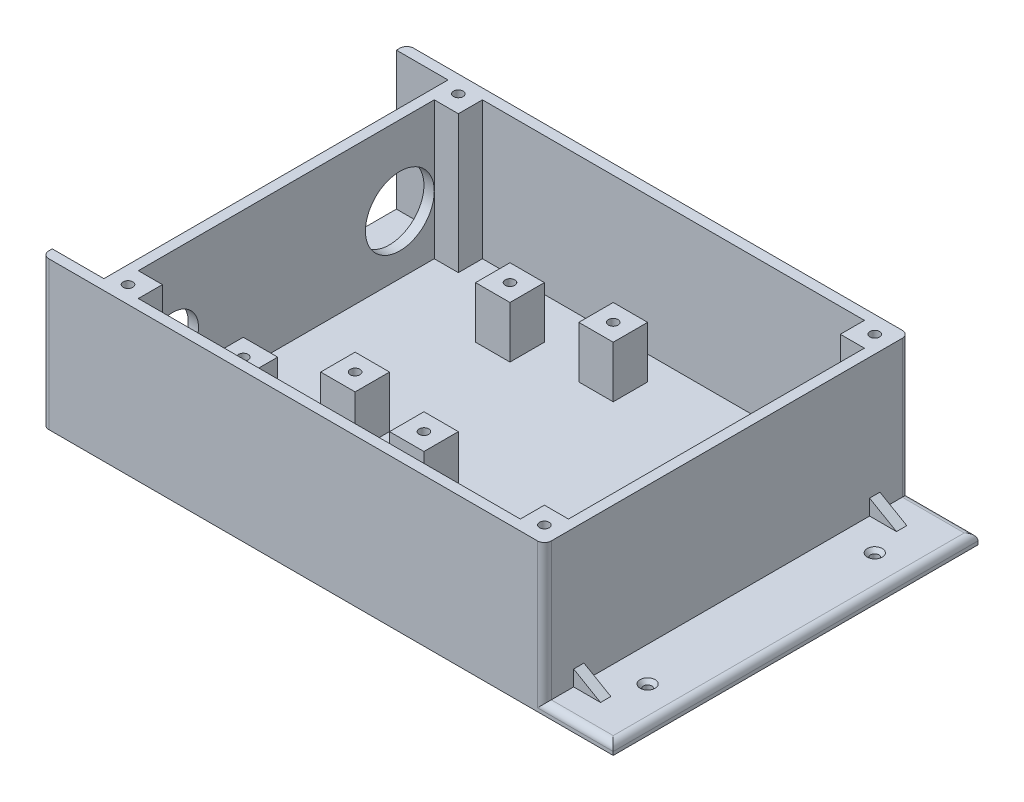
SolidWorks part; units mm, degrees
ref_plane "Front Plane" through (0, 0, 0) normal (0, 0, 1) x (1, 0, 0)
ref_plane "Top Plane" through (0, 0, 0) normal (0, 1, 0) x (1, 0, 0)
ref_plane "Right Plane" through (0, 0, 0) normal (1, 0, 0) x (0, 0, -1)
sketch "Sketch1" plane through (0, 0, 0) normal (0, 1, 0) x (1, 0, 0)
  line L1 (0, 0) -> (166, 0)
  line L2 (0, 0) -> (0, 106)
  line L3 (0, 106) -> (166, 106)
  line L4 (166, 0) -> (166, 106)
  dimension "D1" = 106
  dimension "D2" = 166
extrude "Boss-Extrude1" add sketch "Sketch1" along normal blind 43
shell "Shell1" thickness 3
sketch "Sketch2" plane through (0, 3, 0) normal (0, 1, 0) x (1, 0, 0)
  line L0 (166, 103) -> (0, 103) construction
  line L1 (18, 103) -> (15, 103)
  line L2 (18, 103) -> (18, 3)
  line L3 (18, 3) -> (15, 3)
  line L4 (15, 103) -> (15, 3)
  line L5 (0, 103) -> (0, 3) construction
  line L6 (0, 3) -> (166, 3) construction
  point P10 (16.5, 3)
  dimension "D1" = 15
  dimension "D2" = 3
extrude "Boss-Extrude2" add sketch "Sketch2" along normal blind 40
sketch "Sketch3" plane through (15, 0, 0) normal (-1, 0, 0) x (0, 0, 1)
  line L0 (-106, 0) -> (0, 0) construction
  line L1 (-106, 43) -> (-106, 0) construction
  circle A0 centre (-86, 20) radius 10
  dimension "D1" = 20
  dimension "D2" = 20
extrude "Cut-Extrude1" cut sketch "Sketch3" against normal blind 3
sketch "Sketch4" plane through (15, 0, 0) normal (-1, 0, 0) x (0, 0, 1)
  line L0 (0, 43) -> (0, 0) construction
  line L3 (-106, 0) -> (0, 0) construction
  circle A0 centre (-20, 20) radius 7.5
  dimension "D1" = 20
  dimension "D2" = 20
extrude "Cut-Extrude3" cut sketch "Sketch4" against normal blind 3
sketch "Sketch5" plane through (0, 3, 0) normal (0, 1, 0) x (1, 0, 0)
  line L1 (146, 103) -> (143, 103)
  line L2 (146, 103) -> (146, 3)
  line L3 (146, 3) -> (143, 3)
  line L4 (143, 103) -> (143, 3)
  line L5 (18, 3) -> (166, 3) construction
  line L6 (166, 103) -> (18, 103) construction
  line L7 (166, 3) -> (166, 103) construction
  point P4 (144.5, 103)
  dimension "D1" = 3
  dimension "D2" = 20
extrude "Boss-Extrude4" add sketch "Sketch5" along normal blind 40
sketch "Sketch6" plane through (166, 0, 0) normal (1, 0, 0) x (0, 0, -1)
  line L0 (106, 43) -> (106, 0) construction
  line L1 (106, 3) -> (103, 3)
  line L2 (106, 3) -> (106, 43)
  line L3 (106, 43) -> (103, 43)
  line L4 (103, 3) -> (103, 43)
  line L5 (103, 43) -> (106, 43) construction
  point P8 (104.5, 43)
  dimension "D1" = 3
  dimension "D2" = 40
extrude "Cut-Extrude4" cut sketch "Sketch6" against normal blind 20
ref_plane "Plane5" through (0, 0, -53) normal (0, 0, -1) x (-1, 0, 0)
mirror "Mirror1" about plane through (0, 0, -53) normal (0, 0, -1) of "Cut-Extrude4"
hole_wizard "CSK for #2 Flat Head Machine Screw1" positions "3DSketch2" profile "Sketch12" countersink size "#2" standard "ANSI Inch" end condition through all
sketch3d "3DSketch2"
  line L0 (146, 3, -106) -> (166, 3, -106) construction
  line L1 (166, 3, 0) -> (166, 3, -106) construction
  line L2 (146, 3, 0) -> (166, 3, 0) construction
  point P0 (156, 3, -86)
  point P2 (156, 3, -20)
  dimension "D1" = 20
  dimension "D2" = 10
  dimension "D3" = 10
  dimension "D4" = 20
sketch "Sketch12" plane through (156, 3, -86) normal (1, 0, 0) x (0, 0, 1)
  line L0 (0, 0) -> (0, 3)
  line L1 (0, 3) -> (1.2192, 3)
  line L2 (1.2192, 3) -> (1.2192, 1.1103)
  line L3 (1.2192, 1.1103) -> (2.1844, 0)
  line L5 (2.1844, 0) -> (0, 0)
  line L6 (-1.2192, 1.1103) -> (-2.1844, 0) construction
  line L11 (0, -6.35) -> (0, 107.95) construction
  dimension "Thru Hole Dia." = 2.4384
  dimension "Thru Hole Depth" = 3
  dimension "Near C'Sink Dia." = 4.3688
  dimension "Near C'Sink Angle" = 82
hole_wizard "CSK for #2 Flat Head Machine Screw2" positions "Sketch13" profile "Sketch14" countersink size "#2" standard "ANSI Inch" end condition through all
sketch "Sketch13" plane through (0, 3, 0) normal (0, 1, 0) x (1, 0, 0)
  line L0 (146, 106) -> (0, 106) construction
  line L1 (0, 103) -> (0, 3) construction
  line L2 (0, 0) -> (146, 0) construction
  point P0 (7.5, 20)
  point P2 (7.5, 86)
  dimension "D1" = 20
  dimension "D2" = 7.5
  dimension "D3" = 20
  dimension "D4" = 7.5
sketch "Sketch14" plane through (7.5, 3, -20) normal (1, 0, 0) x (0, 0, 1)
  line L0 (0, 0) -> (0, 3)
  line L1 (0, 3) -> (1.2192, 3)
  line L2 (1.2192, 3) -> (1.2192, 1.1103)
  line L3 (1.2192, 1.1103) -> (2.1844, 0)
  line L5 (2.1844, 0) -> (0, 0)
  line L6 (-1.2192, 1.1103) -> (-2.1844, 0) construction
  line L11 (0, -6.35) -> (0, 107.95) construction
  dimension "Thru Hole Dia." = 2.4384
  dimension "Thru Hole Depth" = 3
  dimension "Near C'Sink Dia." = 4.3688
  dimension "Near C'Sink Angle" = 82
ref_plane "Plane6" through (0, 0, -96) normal (0, 0, -1) x (-1, 0, 0)
sketch "Sketch16" plane through (0, 0, -96) normal (0, 0, -1) x (-1, 0, 0)
  line L0 (-153.8156, 3) -> (-146, 7.5123)
  line L1 (-146, 3) -> (-146, 43) construction
  line L2 (-146, 7.5123) -> (-146, 3)
  line L3 (-146, 3) -> (-166, 3) construction
  line L4 (-146, 3) -> (-153.8156, 3)
  dimension "D1" = 30
extrude "Boss-Extrude6" add sketch "Sketch16" along normal mid plane 3
mirror "Mirror2" about plane through (0, 0, -53) normal (0, 0, -1) of "Boss-Extrude6"
sketch "Sketch17" plane through (0, 3, 0) normal (0, 1, 0) x (1, 0, 0)
  line L1 (143, 103) -> (136, 103)
  line L2 (143, 103) -> (143, 96)
  line L3 (143, 96) -> (136, 96)
  line L4 (136, 103) -> (136, 96)
  dimension "D1" = 7
  dimension "D2" = 7
extrude "Boss-Extrude7" add sketch "Sketch17" along normal blind 40
ref_plane "Plane7" through (80.5, 0, 0) normal (-1, 0, 0) x (0, 0, 1)
sketch "Sketch20" plane through (0, 3, 0) normal (0, 1, 0) x (1, 0, 0)
  line L0 (146, 106) -> (0, 106) construction
  line L1 (143, 96) -> (133, 96)
  line L2 (143, 96) -> (143, 86)
  line L3 (143, 86) -> (133, 86)
  line L4 (133, 96) -> (133, 86)
  line L5 (146, 0) -> (146, 106) construction
  dimension "D1" = 10
  dimension "D2" = 10
  dimension "D3" = 10
  dimension "D4" = 3
extrude "Boss-Extrude8" add sketch "Sketch20" along normal blind 15
sketch "Sketch21" plane through (0, 3, 0) normal (0, 1, 0) x (1, 0, 0)
  line L0 (0, 0) -> (146, 0) construction
  line L1 (35, 33.5) -> (25, 33.5)
  line L2 (35, 33.5) -> (35, 23.5)
  line L3 (35, 23.5) -> (25, 23.5)
  line L4 (25, 33.5) -> (25, 23.5)
  line L5 (15, 103) -> (15, 3) construction
  dimension "D1" = 10
  dimension "D2" = 10
  dimension "D3" = 23.5
  dimension "D4" = 10
extrude "Boss-Extrude9" add sketch "Sketch21" along normal blind 15
sketch "Sketch22" plane through (0, 3, 0) normal (0, 1, 0) x (1, 0, 0)
  line L0 (0, 0) -> (146, 0) construction
  line L1 (69, 17.5) -> (59, 17.5)
  line L2 (69, 17.5) -> (69, 7.5)
  line L3 (69, 7.5) -> (59, 7.5)
  line L4 (59, 17.5) -> (59, 7.5)
  line L5 (15, 103) -> (15, 3) construction
  dimension "D1" = 10
  dimension "D2" = 10
  dimension "D3" = 7.5
  dimension "D4" = 44
extrude "Boss-Extrude10" add sketch "Sketch22" along normal blind 15
sketch "Sketch23" plane through (0, 3, 0) normal (0, 1, 0) x (1, 0, 0)
  line L0 (15, 103) -> (15, 3) construction
  line L1 (55, 91) -> (45, 91)
  line L2 (55, 91) -> (55, 81)
  line L3 (55, 81) -> (45, 81)
  line L4 (45, 91) -> (45, 81)
  line L6 (146, 106) -> (0, 106) construction
  point P6 (50, 91)
  dimension "D1" = 10
  dimension "D2" = 10
  dimension "D3" = 30
  dimension "D4" = 15
extrude "Boss-Extrude11" add sketch "Sketch23" along normal blind 15
sketch "Sketch24" plane through (0, 3, 0) normal (0, 1, 0) x (1, 0, 0)
  line L1 (55, 46) -> (45, 46)
  line L2 (55, 46) -> (55, 36)
  line L3 (55, 36) -> (45, 36)
  line L4 (45, 46) -> (45, 36)
  line L6 (15, 103) -> (15, 3) construction
  line L7 (146, 106) -> (0, 106) construction
  point P4 (45, 41)
  dimension "D1" = 10
  dimension "D2" = 10
  dimension "D3" = 30
  dimension "D4" = 60
extrude "Boss-Extrude12" add sketch "Sketch24" along normal blind 15
sketch "Sketch25" plane through (0, 3, 0) normal (0, 1, 0) x (1, 0, 0)
  line L0 (146, 106) -> (0, 106) construction
  line L1 (143, 41) -> (133, 41)
  line L2 (143, 41) -> (143, 31)
  line L3 (143, 31) -> (133, 31)
  line L4 (133, 41) -> (133, 31)
  line L5 (146, 0) -> (146, 106) construction
  dimension "D1" = 10
  dimension "D2" = 10
  dimension "D3" = 65
  dimension "D4" = 3
extrude "Boss-Extrude13" add sketch "Sketch25" along normal blind 15
sketch "Sketch26" plane through (0, 3, 0) normal (0, 1, 0) x (1, 0, 0)
  line L0 (146, 106) -> (0, 106) construction
  line L1 (80, 96) -> (70, 96)
  line L2 (80, 96) -> (80, 86)
  line L3 (80, 86) -> (70, 86)
  line L4 (70, 96) -> (70, 86)
  line L5 (146, 0) -> (146, 106) construction
  dimension "D1" = 10
  dimension "D2" = 10
  dimension "D3" = 10
  dimension "D4" = 66
extrude "Boss-Extrude14" add sketch "Sketch26" along normal blind 15
sketch "Sketch27" plane through (0, 3, 0) normal (0, 1, 0) x (1, 0, 0)
  line L0 (146, 106) -> (0, 106) construction
  line L1 (80, 41) -> (70, 41)
  line L2 (80, 41) -> (80, 31)
  line L3 (80, 31) -> (70, 31)
  line L4 (70, 41) -> (70, 31)
  line L5 (146, 0) -> (146, 106) construction
  dimension "D1" = 10
  dimension "D2" = 10
  dimension "D3" = 65
  dimension "D4" = 66
extrude "Boss-Extrude15" add sketch "Sketch27" along normal blind 15
sketch "Sketch28" plane through (0, 43, 0) normal (0, 1, 0) x (1, 0, 0)
  line L0 (146, 0) -> (146, 106) construction
  line L1 (146, 106) -> (0, 106) construction
  circle A0 centre (141, 101) radius 1.4
  dimension "D1" = 5
  dimension "D2" = 5
extrude "Cut-Extrude5" cut sketch "Sketch28" against normal blind 10
mirror "Mirror3" about plane through (0, 0, -53) normal (0, 0, -1) of "Cut-Extrude5", "Boss-Extrude7"
mirror "Mirror4" about plane through (80.5, 0, 0) normal (-1, 0, 0) of "Mirror3", "Boss-Extrude7", "Cut-Extrude5"
fillet "Fillet2" radius 2 4 edges at (0, 21.5, -106) (146, 23, -106) (146, 23, 0) (0, 21.5, 0)
fillet "Fillet3" radius 2 3 edges at (155, 3, 0) (155, 3, -106) (166, 3, -53)
sketch "Sketch29" plane through (0, 18, 0) normal (0, 1, 0) x (1, 0, 0)
  line L0 (143, 86) -> (143, 96) construction
  line L1 (133, 86) -> (143, 86) construction
  circle A0 centre (138, 91) radius 1.4
  dimension "D1" = 5
  dimension "D2" = 5
extrude "Cut-Extrude6" cut sketch "Sketch29" against normal blind 10
ref_plane "Plane8" through (0, 0, -63.5) normal (0, 0, -1) x (-1, 0, 0)
ref_plane "Plane9" through (106.5, 0, 0) normal (-1, 0, 0) x (0, 0, 1)
mirror "Mirror5" about plane through (0, 0, -63.5) normal (0, 0, -1) of "Cut-Extrude6"
mirror "Mirror6" about plane through (106.5, 0, 0) normal (-1, 0, 0) of "Mirror5", "Cut-Extrude6"
sketch "Sketch30" plane through (0, 18, 0) normal (0, 1, 0) x (1, 0, 0)
  line L0 (55, 81) -> (55, 91) construction
  line L1 (45, 81) -> (55, 81) construction
  circle A0 centre (50, 86) radius 1.4
  dimension "D1" = 5
  dimension "D2" = 5
extrude "Cut-Extrude7" cut sketch "Sketch30" against normal blind 10
ref_plane "Plane10" through (0, 0, -63.5) normal (0, 0, 1) x (1, 0, 0)
mirror "Mirror7" about plane through (0, 0, -63.5) normal (0, 0, 1) of "Cut-Extrude7"
sketch "Sketch31" plane through (0, 18, 0) normal (0, 1, 0) x (1, 0, 0)
  line L0 (69, 7.5) -> (69, 17.5) construction
  line L1 (59, 7.5) -> (69, 7.5) construction
  circle A0 centre (64, 12.5) radius 1.4
  dimension "D1" = 5
  dimension "D2" = 5
extrude "Cut-Extrude8" cut sketch "Sketch31" against normal blind 10
sketch "Sketch32" plane through (0, 18, 0) normal (0, 1, 0) x (1, 0, 0)
  line L0 (35, 23.5) -> (35, 33.5) construction
  line L1 (25, 23.5) -> (35, 23.5) construction
  circle A0 centre (30, 28.5) radius 1.4
  dimension "D1" = 5
  dimension "D2" = 5
extrude "Cut-Extrude9" cut sketch "Sketch32" against normal blind 10
